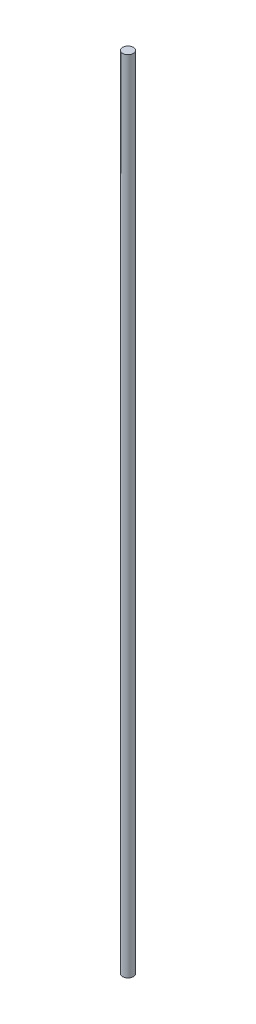
SolidWorks part; units mm, degrees
material "Cast Carbon Steel"
ref_plane "Front Plane" through (0, 0, 0) normal (0, 0, 1) x (1, 0, 0)
ref_plane "Top Plane" through (0, 0, 0) normal (0, 1, 0) x (1, 0, 0)
ref_plane "Right Plane" through (0, 0, 0) normal (1, 0, 0) x (0, 0, -1)
sketch "Sketch1" plane through (0, 0, 0) normal (0, 1, 0) x (1, 0, 0)
  circle A0 centre (0, 0) radius 4
  dimension "D1" = 8
extrude "Boss-Extrude1" add sketch "Sketch1" along normal blind 600
sketch "Sketch2" plane through (0, 0, 0) normal (0, -1, 0) x (-1, 0, 0)
  circle A0 centre (0, 0) radius 3
  dimension "D1" = 6
